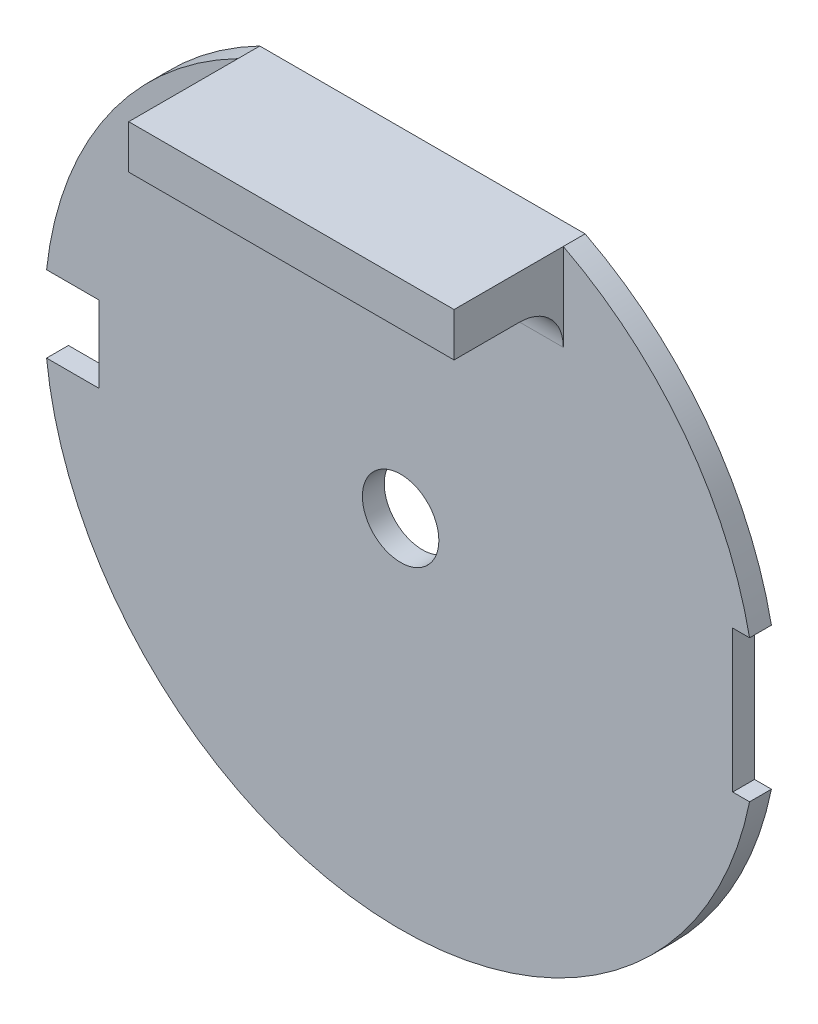
SolidWorks part; units mm, degrees
ref_plane "前视基准面" through (0, 0, 0) normal (0, 0, 1) x (1, 0, 0)
ref_plane "上视基准面" through (0, 0, 0) normal (0, 1, 0) x (1, 0, 0)
ref_plane "右视基准面" through (0, 0, 0) normal (1, 0, 0) x (0, 0, -1)
sketch "草图1" plane through (0, 0, 0) normal (0, 0, 1) x (1, 0, 0)
  line L0 (-7.4458, 14.5) -> (7.4458, 14.5)
  arc A0 (-7.4458, 14.5) -> (7.4458, 14.5) centre (0, 0) ccw
  circle A1 centre (0, 0) radius 1.75
  dimension "D1" = 32.6
  dimension "D2" = 3.5
  dimension "D3" = 14.5
extrude "凸台-拉伸1" add sketch "草图1" along normal blind 1
sketch "草图2" plane through (0, 0, 1) normal (0, 0, 1) x (1, 0, 0)
  line L0 (-13.8, 1.75) -> (15.2, 1.75) construction
  line L1 (-18.8, 1.75) -> (-13.8, 1.75)
  line L2 (-18.8, 1.75) -> (-18.8, -1.75)
  line L3 (-18.8, -1.75) -> (-13.8, -1.75)
  line L4 (-13.8, 1.75) -> (-13.8, -1.75)
  line L5 (15.2, 1.75) -> (17.8078, 1.75) construction
  line L6 (15.2, 1.75) -> (15.2, -1.75) construction
  line L7 (15.2, -1.75) -> (17.8078, -1.75) construction
  line L8 (17.8078, 1.75) -> (17.8078, -1.75) construction
  line L9 (15.2, -1.75) -> (-13.8, -1.75) construction
  line L11 (15.2, 3.25) -> (17.2, 3.25)
  line L12 (15.2, 3.25) -> (15.2, -3.25)
  line L13 (15.2, -3.25) -> (17.2, -3.25)
  line L14 (17.2, 3.25) -> (17.2, -3.25)
  circle A0 centre (0, 0) radius 16.3 construction
  point P10 (-16.3, 0)
  point P11 (16.3, 0)
  point P13 (-13.8, 0)
  point P17 (17.2, 0)
  dimension "D1" = 29
  dimension "D2" = 2.5
  dimension "D3" = 5
  dimension "D4" = 3.5
  dimension "D5" = 6.5
  dimension "D6" = 2
extrude "切除-拉伸1" cut sketch "草图2" against normal through all
sketch "草图3" plane through (0, 0, 1) normal (0, 0, 1) x (1, 0, 0)
  line L1 (-7.4458, 14.5) -> (7.4458, 14.5)
  line L2 (-7.4458, 14.5) -> (-7.4458, 12.5)
  line L3 (-7.4458, 12.5) -> (7.4458, 12.5)
  line L4 (7.4458, 14.5) -> (7.4458, 12.5)
  dimension "D1" = 2
extrude "凸台-拉伸2" add sketch "草图3" along normal blind 5
fillet "圆角1" radius 2 1 edges at (0, 12.5, 1)
